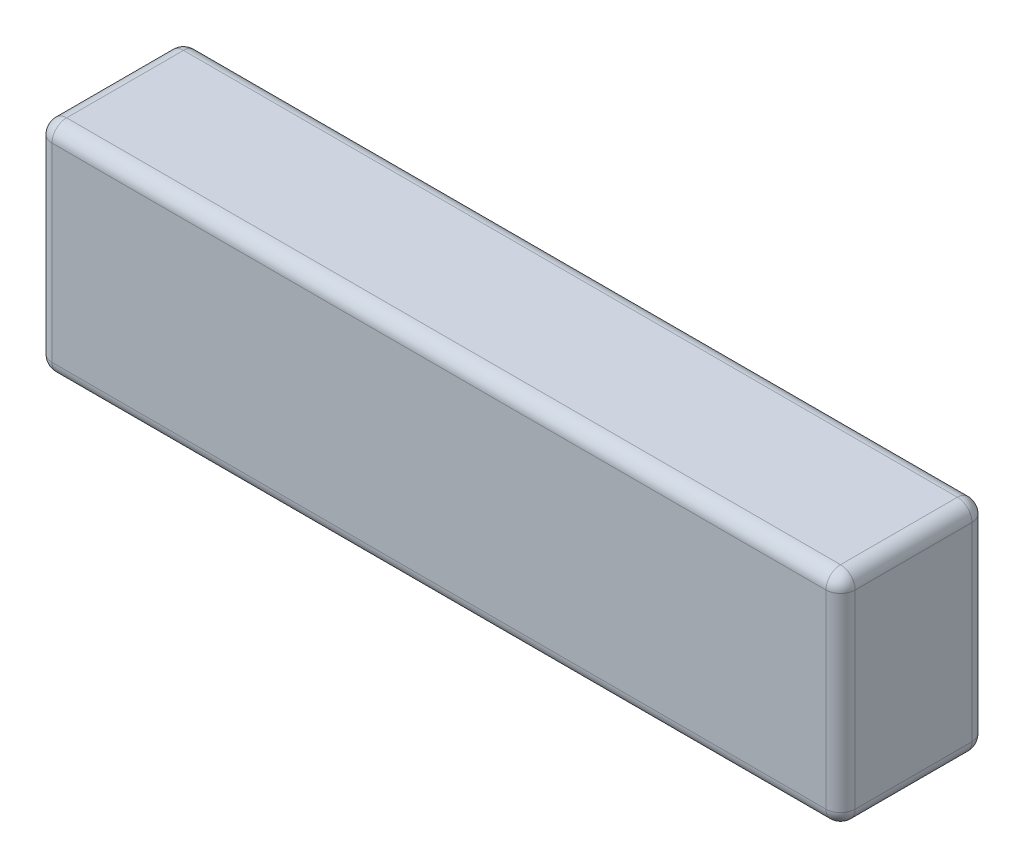
SolidWorks part; units mm, degrees
material "battery "
ref_plane "Front Plane" through (0, 0, 0) normal (0, 0, 1) x (1, 0, 0)
ref_plane "Top Plane" through (0, 0, 0) normal (0, 1, 0) x (1, 0, 0)
ref_plane "Right Plane" through (0, 0, 0) normal (1, 0, 0) x (0, 0, -1)
sketch "Sketch1" plane through (0, 0, 0) normal (0, 0, 1) x (1, 0, 0)
  line L1 (-82.5, 22.5) -> (82.5, 22.5)
  line L2 (-82.5, 22.5) -> (-82.5, -22.5)
  line L3 (-82.5, -22.5) -> (82.5, -22.5)
  line L4 (82.5, 22.5) -> (82.5, -22.5)
  line L5 (-82.5, 22.5) -> (82.5, -22.5) construction
  line L6 (-82.5, -22.5) -> (82.5, 22.5) construction
  point P0 (0, 0)
  dimension "D1" = 165
  dimension "D2" = 45
extrude "Boss-Extrude1" add sketch "Sketch1" along normal blind 30
fillet "Fillet1" radius 3 12 edges at (82.5, 22.5, 15) (82.5, -22.5, 15) (82.5, 0, 30) (82.5, 0, 0) (0, -22.5, 0) (0, -22.5, 30) (0, 22.5, 0) (0, 22.5, 30) (-82.5, 22.5, 15) (-82.5, 0, 0) (-82.5, -22.5, 15) (-82.5, 0, 30)
sketch "Sketch3" plane through (0, 0, 0) normal (0, 0, -1) x (-1, 0, 0)
  text T0 "SkyCell 11.1V" font "Century Gothic" height 3.5
extrude "Cut-Extrude1" cut sketch "Sketch3" against normal blind 1
